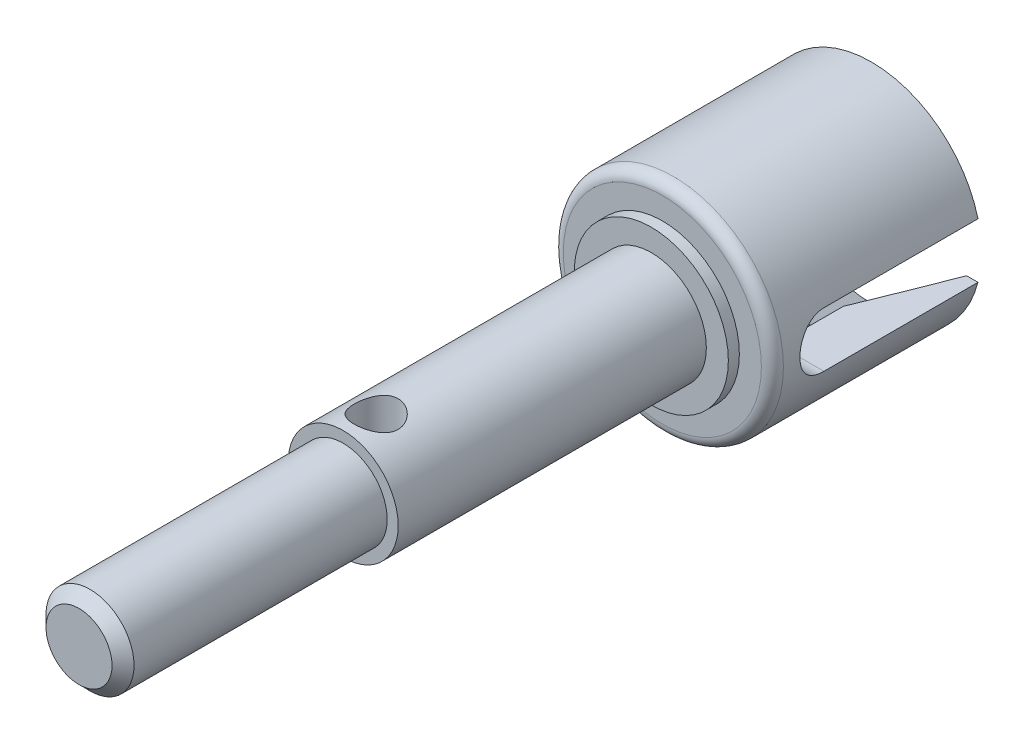
SolidWorks part; units mm, degrees
ref_plane "Plane1" through (0, 0, 0) normal (0, 0, 1) x (1, 0, 0)
ref_plane "Plane2" through (0, 0, 0) normal (0, 1, 0) x (1, 0, 0)
ref_plane "Plane3" through (0, 0, 0) normal (1, 0, 0) x (0, 0, -1)
sketch "Esquisse1" plane through (0, 0, 0) normal (0, 0, 1) x (1, 0, 0)
  circle A0 centre (0, 0) radius 5
  dimension "D1" = 10
extrude "Base-Extrusion" add sketch "Esquisse1" along normal blind 9.5
sketch "Esquisse2" plane through (0, 0, 9.5) normal (0, 0, 1) x (1, 0, 0)
  circle A0 centre (0, 0) radius 3.5
  dimension "D1" = 7
extrude "Boss.-Extru.1" add sketch "Esquisse2" along normal blind 0.5
sketch "Esquisse3" plane through (0, 0, 10) normal (0, 0, 1) x (1, 0, 0)
  circle A0 centre (0, 0) radius 2.5
  dimension "D1" = 5
extrude "Boss.-Extru.2" add sketch "Esquisse3" along normal blind 14
sketch "Esquisse4" plane through (0, 0, 24) normal (0, 0, 1) x (1, 0, 0)
  circle A0 centre (0, 0) radius 2
  dimension "D1" = 4
extrude "Boss.-Extru.3" add sketch "Esquisse4" along normal blind 12
chamfer "Chanfrein1" distance 0.5 angle 45
fillet "Congé1" radius 0.5
sketch "Esquisse7" plane through (0, 0, 0) normal (1, 0, 0) x (0, 0, -1)
  line L0 (0, 0) -> (-11.8343, 0) construction
  line L1 (-9, 0) -> (0, 0) construction
  line L2 (1, 1.25) -> (-7, 1.25)
  line L3 (1, -1.25) -> (-7, -1.25)
  line L4 (-7, 1.25) -> (-7, -1.25) construction
  line L5 (0, -5) -> (0, 5) construction
  line L6 (1, 1.25) -> (1, -1.25)
  arc A0 (-7, 1.25) -> (-7, -1.25) centre (-7, 0) ccw
  dimension "D1" = 7
  dimension "D2" = 2.5
extrude "Enlèv. mat.-Extru.1" cut sketch "Esquisse7" against normal mid plane 32
sketch "Esquisse8" plane through (0, 0, 0) normal (1, 0, 0) x (0, 0, -1)
  line L0 (0, 4.5) -> (-4, 3)
  line L1 (0, 1.25) -> (0, 5) construction
  line L2 (-4, 3) -> (-8, 3)
  line L3 (-8, 3) -> (-9.5, 0)
  line L4 (-9, 0) -> (0, 0) construction
  line L5 (-9.5, 0) -> (0, 0)
  line L6 (0, 0) -> (0, 4.5)
  line L7 (0, 0) -> (-14.7422, 0) construction
  dimension "D1" = 4
  dimension "D2" = 3
  dimension "D3" = 4
  dimension "D4" = 1.5
  dimension "D5" = 4.5
revolve "Enlèvement de matière-Révolution1" cut sketch "Esquisse8" angle 360 about L7
sketch "Esquisse9" plane through (0, 0, 0) normal (0, 1, 0) x (1, 0, 0)
  line L0 (0, 0) -> (0, -37.0244) construction
  line L1 (0, -9) -> (0, 0) construction
  line L2 (-3.5, -10) -> (3.5, -10) construction
  circle A0 centre (0, -22.5) radius 1
  dimension "D1" = 2
  dimension "D2" = 12.5
extrude "Enlèv. mat.-Extru.2" cut sketch "Esquisse9" against normal mid plane 20
